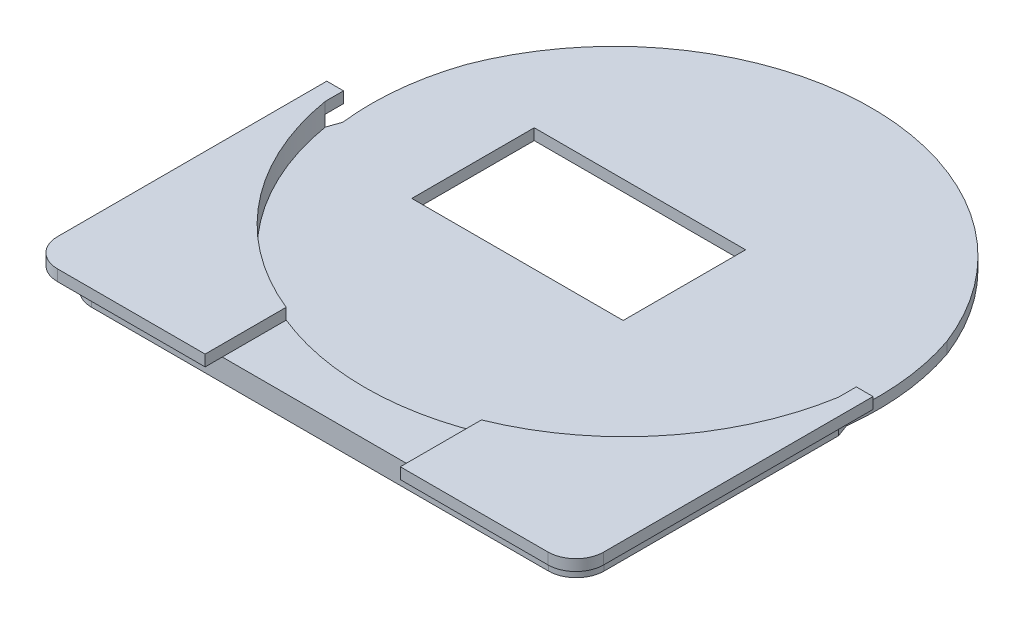
SolidWorks part; units mm, degrees
ref_plane "Front Plane" through (0, 0, 0) normal (0, 0, 1) x (1, 0, 0)
ref_plane "Top Plane" through (0, 0, 0) normal (0, 1, 0) x (1, 0, 0)
ref_plane "Right Plane" through (0, 0, 0) normal (1, 0, 0) x (0, 0, -1)
sketch "Sketch4" plane through (0, 0, 0) normal (0, 1, 0) x (1, 0, 0)
  line L1 (-107.0357, 49.142) -> (-15.0357, 49.142)
  line L2 (-107.0357, 49.142) -> (-107.0357, -45.858)
  line L3 (-102.0357, -50.858) -> (-20.0357, -50.858)
  line L4 (-15.0357, 49.142) -> (-15.0357, -45.858)
  arc A0 (-20.0357, -50.858) -> (-15.0357, -45.858) centre (-20.0357, -45.858) ccw
  arc A1 (-107.0357, -45.858) -> (-102.0357, -50.858) centre (-102.0357, -45.858) ccw
  point P6 (-15.0357, -50.858)
  point P9 (-107.0357, -50.858)
  dimension "D3" = 5
  dimension "D1" = 92
  dimension "D2" = 100
extrude "Boss-Extrude2" add sketch "Sketch4" along normal blind 4
sketch "Sketch5" plane through (0, 4, 0) normal (0, 1, 0) x (1, 0, 0)
  line L1 (-122.1841, 54.3122) -> (-0.8811, 54.3122)
  line L3 (-122.1841, 54.3122) -> (-116.2059, -1.7638)
  line L4 (-116.2059, -1.7638) -> (-107.0357, -1.7638)
  line L5 (-15.0357, -1.7638) -> (-0.8811, -1.7638)
  line L6 (-0.8811, -1.7638) -> (-0.8811, 54.3122)
  line L7 (-107.0357, 49.142) -> (-107.0357, -45.858) construction
  line L8 (-15.0357, -45.858) -> (-15.0357, 49.142) construction
  arc A0 (-15.0357, -1.7638) -> (-107.0357, -1.7638) centre (-61.0357, 1.9398) ccw
extrude "Cut-Extrude3" cut sketch "Sketch5" against normal blind 4
sketch "Sketch6" plane through (0, 4, 0) normal (0, 1, 0) x (1, 0, 0)
  circle A1 centre (-61.0392, 3.842) radius 46.6449
extrude "Cut-Extrude4" cut sketch "Sketch6" against normal blind 2
sketch "Sketch7" plane through (0, 2, 0) normal (0, 1, 0) x (1, 0, 0)
  line L1 (-50.2681, 14.744) -> (-88.1898, 14.744)
  line L2 (-50.2681, 14.744) -> (-50.2681, -7.222)
  line L3 (-50.2681, -7.222) -> (-88.1898, -7.222)
  line L4 (-88.1898, 14.744) -> (-88.1898, -7.222)
extrude "Cut-Extrude5" cut sketch "Sketch7" against normal blind 2
sketch "Sketch13" plane through (0, 2, 0) normal (0, 1, 0) x (1, 0, 0)
  line L3 (-106.2173, -1.561) -> (-107.0357, -3.9084)
  line L4 (-107.0357, 5.6435) -> (-107.0357, -3.9084) construction
  line L5 (-107.0357, -3.9084) -> (-110.1181, -1.561)
  line L6 (-15.8612, -1.561) -> (-15.0357, -3.8163)
  line L7 (-15.0357, -3.8667) -> (-15.0357, 5.6435) construction
  line L8 (-15.0357, -3.8163) -> (-11.9604, -1.561)
  arc A0 (-11.9604, -1.561) -> (-110.1181, -1.561) centre (-61.0392, 3.842) ccw
  arc A1 (-15.8612, -1.561) -> (-106.2173, -1.561) centre (-61.0392, 3.842) ccw
extrude "Cut-Extrude7" cut sketch "Sketch13" against normal blind 10
sketch "Sketch10" plane through (0, 4, 0) normal (0, 1, 0) x (1, 0, 0)
  line L0 (-110.0357, -0.1264) -> (-110.0357, -48.858) construction
  line L1 (-110.0357, -0.6264) -> (-107.0357, -0.6264)
  line L2 (-110.0357, -0.6264) -> (-110.0357, -48.9393)
  line L3 (-105.0357, -53.9393) -> (-78.5477, -53.9393)
  line L4 (-12.0357, -0.6264) -> (-12.0357, -48.9393)
  line L6 (-110.0357, -0.1264) -> (-106.6168, -0.1264) construction
  line L8 (-107.0357, -3.9084) -> (-107.0357, -0.6264)
  line L9 (-107.0357, -0.1264) -> (-107.0357, -45.858) construction
  line L10 (-15.0357, -3.8667) -> (-15.0357, -0.6264)
  line L11 (-15.0357, -0.6264) -> (-12.0357, -0.6264)
  line L14 (-78.5477, -53.9393) -> (-78.5477, -39.3923)
  line L16 (-43.5308, -53.9393) -> (-43.5308, -39.3923)
  line L20 (-43.5308, -53.9393) -> (-17.0357, -53.9393)
  arc A1 (-107.0357, -3.9084) -> (-78.5477, -39.3923) centre (-61.0392, 3.842) ccw
  arc A3 (-43.5308, -39.3923) -> (-15.0357, -3.8667) centre (-61.0392, 3.842) ccw
  arc A4 (-17.0357, -53.9393) -> (-12.0357, -48.9393) centre (-17.0357, -48.9393) ccw
  arc A5 (-110.0357, -48.9393) -> (-105.0357, -53.9393) centre (-105.0357, -48.9393) ccw
  point P13 (-61.0392, -47.565)
  point P28 (-12.0357, -53.9393)
  dimension "D2" = 5
  dimension "D1" = 0.5
extrude "Boss-Extrude3" add sketch "Sketch10" along normal blind 2
